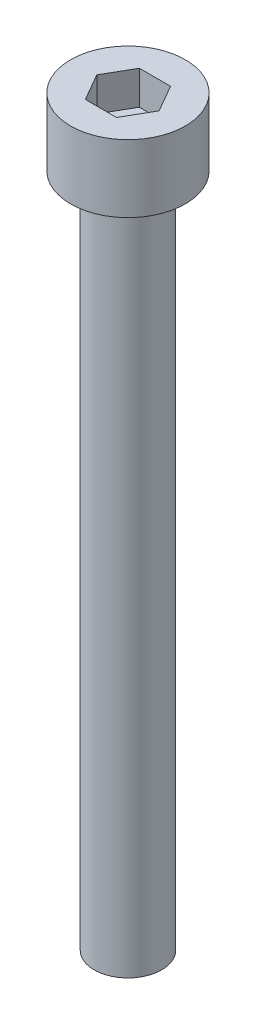
SolidWorks part; units mm, degrees
material "AISI 304"
ref_plane "前视基准面" through (0, 0, 0) normal (0, 0, 1) x (1, 0, 0)
ref_plane "上视基准面" through (0, 0, 0) normal (0, 1, 0) x (1, 0, 0)
ref_plane "右视基准面" through (0, 0, 0) normal (1, 0, 0) x (0, 0, -1)
sketch "草图1" plane through (0, 0, 0) normal (0, 1, 0) x (1, 0, 0)
  circle A0 centre (0, 0) radius 4.25
  dimension "D1" = 8.5
extrude "凸台-拉伸1" add sketch "草图1" along normal blind 5
sketch "草图2" plane through (0, 5, 0) normal (0, 1, 0) x (1, 0, 0)
  line L1 (2.3094, 0) -> (1.1547, 2)
  line L2 (1.1547, 2) -> (-1.1547, 2)
  line L3 (-1.1547, 2) -> (-2.3094, 0)
  line L4 (-2.3094, 0) -> (-1.1547, -2)
  line L5 (-1.1547, -2) -> (1.1547, -2)
  line L6 (1.1547, -2) -> (2.3094, 0)
  circle A0 centre (0, 0) radius 2 construction
  dimension "D1" = 4
extrude "切除-拉伸1" cut sketch "草图2" against normal blind 2.5
sketch "草图3" plane through (0, 0, 0) normal (0, -1, 0) x (1, 0, 0)
  circle A0 centre (0, 0) radius 2.5
  dimension "D1" = 5
extrude "凸台-拉伸2" add sketch "草图3" along normal blind 50
